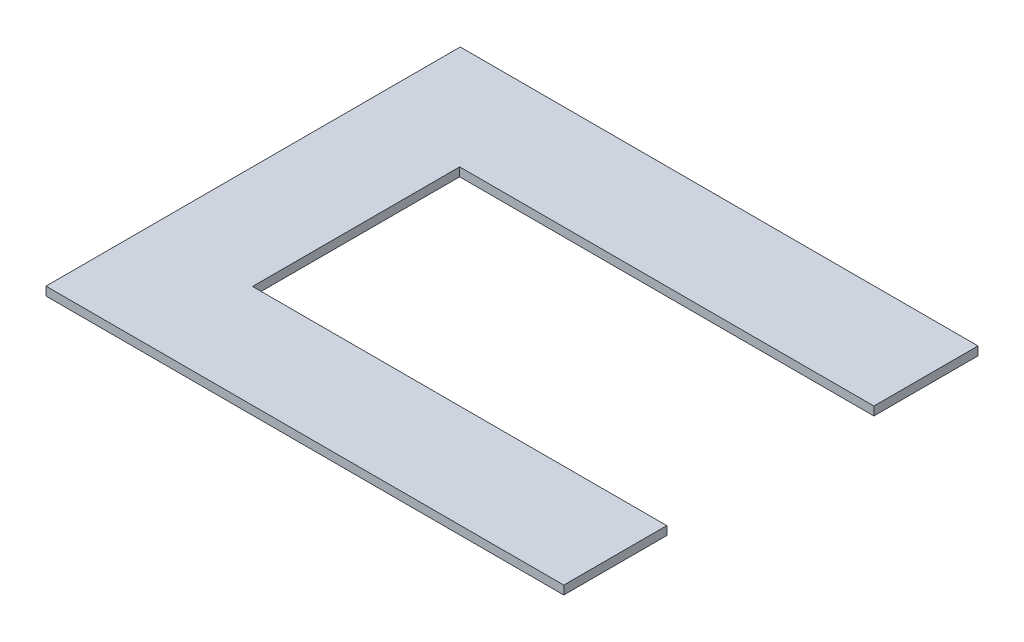
SolidWorks part; units mm, degrees
ref_plane "Front Plane" through (0, 0, 0) normal (0, 0, 1) x (1, 0, 0)
ref_plane "Top Plane" through (0, 0, 0) normal (0, 1, 0) x (1, 0, 0)
ref_plane "Right Plane" through (0, 0, 0) normal (1, 0, 0) x (0, 0, -1)
sketch "Sketch1" plane through (0, 0, 0) normal (0, 1, 0) x (1, 0, 0)
  line L1 (0, 0) -> (-381, 0)
  line L2 (0, 0) -> (0, 304.8)
  line L3 (0, 304.8) -> (-381, 304.8)
  line L4 (-381, 0) -> (-381, 304.8)
  dimension "D1" = 381
  dimension "D2" = 304.8
extrude "Boss-Extrude1" add sketch "Sketch1" along normal blind 6.35
sketch "Sketch3" plane through (0, 6.35, 0) normal (0, 1, 0) x (1, 0, 0)
  line L0 (0, 0) -> (0, 304.8) construction
  line L1 (0, 75.7807) -> (-304.8, 75.7807)
  line L2 (0, 75.7807) -> (0, 228.1807)
  line L3 (0, 228.1807) -> (-304.8, 228.1807)
  line L4 (-304.8, 75.7807) -> (-304.8, 228.1807)
  line L5 (0, 152.4) -> (-381, 152.4) construction
  line L6 (-381, 304.8) -> (-381, 0) construction
  dimension "D1" = 304.8
  dimension "D2" = 152.4
extrude "Cut-Extrude2" cut sketch "Sketch3" against normal blind 6.35 contours L1 L4 L3 L2
